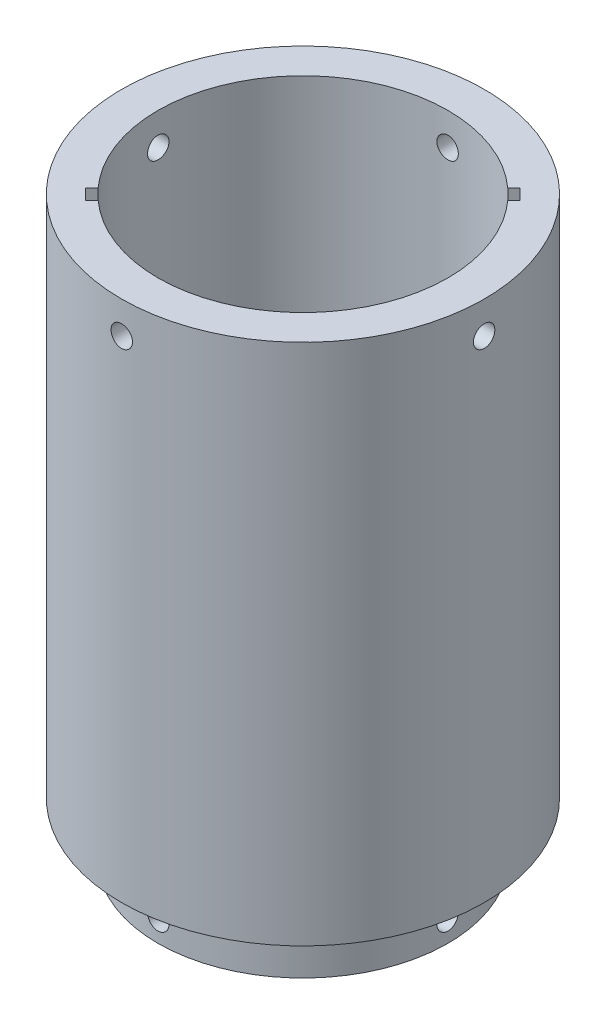
SolidWorks part; units mm, degrees
ref_plane "Front Plane" through (0, 0, 0) normal (0, 0, 1) x (1, 0, 0)
ref_plane "Top Plane" through (0, 0, 0) normal (0, 1, 0) x (1, 0, 0)
ref_plane "Right Plane" through (0, 0, 0) normal (1, 0, 0) x (0, 0, -1)
sketch "Sketch1" plane through (0, 0, 0) normal (0, 1, 0) x (1, 0, 0)
  circle A0 centre (0, 0) radius 33.85
  dimension "D1" = 67.7
extrude "Boss-Extrude1" add sketch "Sketch1" along normal blind 12.5
sketch "Sketch2" plane through (0, 0, 0) normal (1, 0, 0) x (0, 0, -1)
  line L0 (33.85, 12.5) -> (-33.85, 12.5) construction
  circle A0 centre (0, 5) radius 2.5
  dimension "D1" = 5
  dimension "D2" = 7.5
extrude "Cut-Extrude1" cut sketch "Sketch2" against normal through all both and the other way through all
sketch "Sketch3" plane through (0, 0, 0) normal (0, 0, 1) x (1, 0, 0)
  line L0 (33.85, 12.5) -> (-33.85, 12.5) construction
  circle A0 centre (0, 5) radius 2.5
  dimension "D1" = 5
  dimension "D2" = 7.5
extrude "Cut-Extrude2" cut sketch "Sketch3" against normal through all both and the other way through all
sketch "Sketch4" plane through (0, 12.5, 0) normal (0, 1, 0) x (1, 0, 0)
  circle A0 centre (0, 0) radius 42.35
  dimension "D1" = 84.7
extrude "Boss-Extrude2" add sketch "Sketch4" along normal blind 2
sketch "Sketch5" plane through (0, 14.5, 0) normal (0, 1, 0) x (1, 0, 0)
  circle A0 centre (0, 0) radius 33.85 construction
  circle A1 centre (0, 0) radius 42.35
  circle A2 centre (0, 0) radius 42.35
  circle A3 centre (0, 0) radius 33.85
  dimension "D1" = 0
extrude "Boss-Extrude3" add sketch "Sketch5" along normal blind 120
sketch "Sketch6" plane through (0, 0, 0) normal (1, 0, 0) x (0, 0, -1)
  line L0 (42.35, 134.5) -> (-42.35, 134.5) construction
  circle A0 centre (0, 127) radius 2.5
  dimension "D1" = 5
  dimension "D2" = 7.5
extrude "Cut-Extrude3" cut sketch "Sketch6" against normal through all both and the other way through all
sketch "Sketch7" plane through (0, 0, 0) normal (0, 0, 1) x (1, 0, 0)
  line L0 (33.85, 134.5) -> (-33.85, 134.5) construction
  circle A0 centre (0, 127) radius 2.5
  dimension "D1" = 5
  dimension "D2" = 7.5
extrude "Cut-Extrude4" cut sketch "Sketch7" against normal through all both and the other way through all
ref_plane "Plane1" through (0, 12.5, 0) normal (0, 1, 0) x (1, 0, 0)
sketch "Sketch9" plane through (0, 134.5, 0) normal (0, 1, 0) x (1, 0, 0)
  line L0 (24.1123, 26.5872) -> (-26.5872, -24.1123)
  line L5 (-26.5872, -24.1123) -> (-24.1123, -26.5872)
  line L6 (-24.1123, -26.5872) -> (26.5872, 24.1123)
  line L7 (26.5872, 24.1123) -> (24.1123, 26.5872)
  line L8 (-26.5872, -24.1123) -> (26.5872, 24.1123) construction
  line L9 (-24.1123, -26.5872) -> (24.1123, 26.5872) construction
  line L10 (0, 0) -> (-33.85, 0) construction
  line L11 (-25.3498, -25.3498) -> (25.3498, 25.3498) construction
  line L12 (-23.9356, -23.9356) -> (-25.3498, -25.3498) construction
  circle A0 centre (0, 0) radius 33.85 construction
  circle A1 centre (0, 0) radius 33.85 construction
  point P2 (0, 0)
  dimension "D1" = 135
  dimension "D2" = 2
  dimension "D3" = 3.5
extrude "Cut-Extrude5" cut sketch "Sketch9" against normal up to surface (120 mm away) up to face at (0, 14.5, 33.85)
